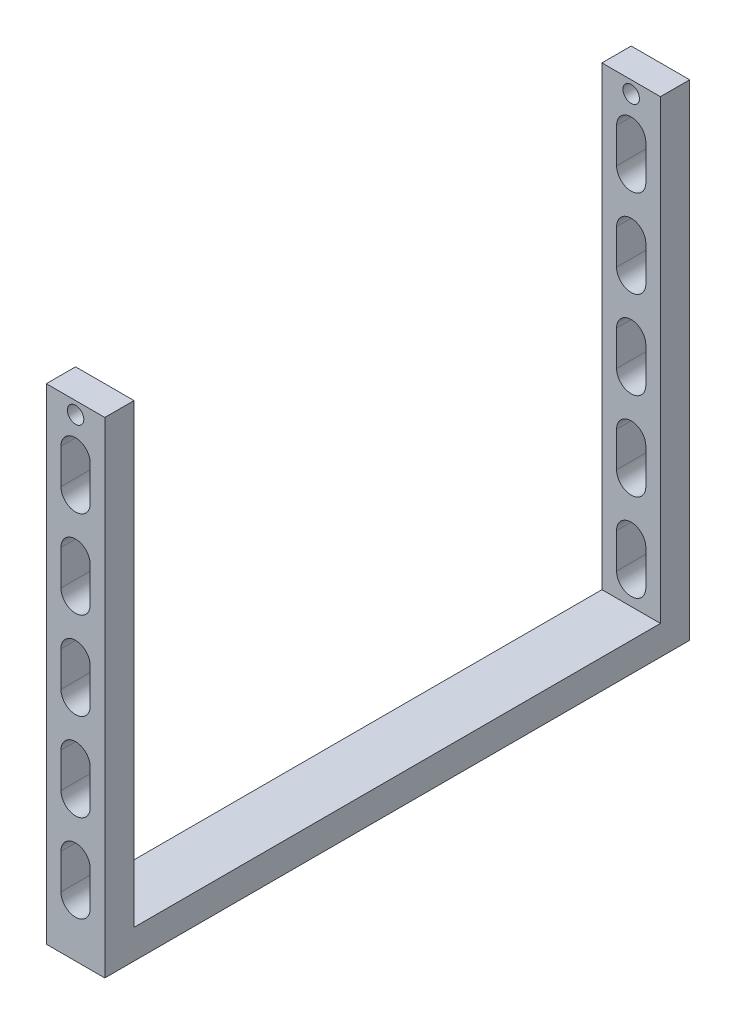
SolidWorks part; units mm, degrees
material "6061 Alloy"
ref_plane "Front Plane" through (0, 0, 0) normal (0, 0, 1) x (1, 0, 0)
ref_plane "Top Plane" through (0, 0, 0) normal (0, 1, 0) x (1, 0, 0)
ref_plane "Right Plane" through (0, 0, 0) normal (1, 0, 0) x (0, 0, -1)
sketch "Sketch1" plane through (0, 0, 0) normal (0, 1, 0) x (1, 0, 0)
  line L1 (-6.35, -3.175) -> (6.35, -3.175)
  line L2 (-6.35, -3.175) -> (-6.35, 3.175)
  line L3 (-6.35, 3.175) -> (6.35, 3.175)
  line L4 (6.35, -3.175) -> (6.35, 3.175)
  line L5 (-6.35, -3.175) -> (6.35, 3.175) construction
  line L6 (-6.35, 3.175) -> (6.35, -3.175) construction
  point P0 (0, 0)
  dimension "D1" = 12.7
  dimension "D2" = 6.35
extrude "Boss-Extrude1" add sketch "Sketch1" against normal blind 105.41
sketch "Sketch2" plane through (0, 0, 3.175) normal (0, 0, 1) x (1, 0, 0)
  line L0 (-6.35, -105.41) -> (-6.35, 0) construction
  line L1 (6.35, -105.41) -> (-6.35, -105.41)
  line L2 (6.35, -105.41) -> (6.35, -99.06)
  line L3 (6.35, -99.06) -> (-6.35, -99.06)
  line L4 (-6.35, -105.41) -> (-6.35, -99.06)
  dimension "D1" = 6.35
extrude "Boss-Extrude2" add sketch "Sketch2" against normal blind 127
sketch "Sketch3" plane through (0, -105.41, 0) normal (0, -1, 0) x (1, 0, 0)
  line L0 (-6.35, -123.825) -> (-6.35, 3.175) construction
  line L1 (6.35, -123.825) -> (-6.35, -123.825)
  line L2 (6.35, -123.825) -> (6.35, -117.475)
  line L3 (6.35, -117.475) -> (-6.35, -117.475)
  line L4 (-6.35, -123.825) -> (-6.35, -117.475)
  dimension "D1" = 6.35
extrude "Boss-Extrude3" add sketch "Sketch3" against normal blind 105.41
sketch "Sketch4" plane through (0, 0, -123.825) normal (0, 0, -1) x (-1, 0, 0)
  line L0 (0, -10.16) -> (0, -17.78) construction
  line L1 (3.175, -10.16) -> (3.175, -17.78)
  line L2 (-3.175, -10.16) -> (-3.175, -17.78)
  arc A0 (3.175, -10.16) -> (-3.175, -10.16) centre (0, -10.16) ccw
  arc A1 (-3.175, -17.78) -> (3.175, -17.78) centre (0, -17.78) ccw
  point P3 (0, -13.97)
  dimension "D2" = 3.175
  dimension "D1" = 7.62
  dimension "D3" = 10.16
extrude "Cut-Extrude1" cut sketch "Sketch4" against normal through all
pattern_linear "LPattern1" count 5 spacing 19.05 along (0, 1, 0) of "Cut-Extrude1"
hole_wizard "9/64 (0.14063) Diameter Hole1" positions "Sketch8" profile "Sketch7" hole size "9/64" standard "Ansi Inch" end condition through all
sketch "Sketch8" plane through (0, 0, -123.825) normal (0, 0, -1) x (-1, 0, 0)
  point P0 (0, -2.667)
  dimension "D1" = 2.667
sketch "Sketch7" plane through (0, -2.667, -123.825) normal (1, 0, 0) x (0, 1, 0)
  line L0 (0, 0) -> (0, 127)
  line L1 (0, 127) -> (1.786, 127)
  line L2 (1.786, 127) -> (1.786, 0)
  line L5 (1.786, 0) -> (0, 0)
  line L11 (0, -6.35) -> (0, 107.95) construction
  dimension "Thru Hole Dia." = 3.572
  dimension "Thru Hole Depth" = 127
